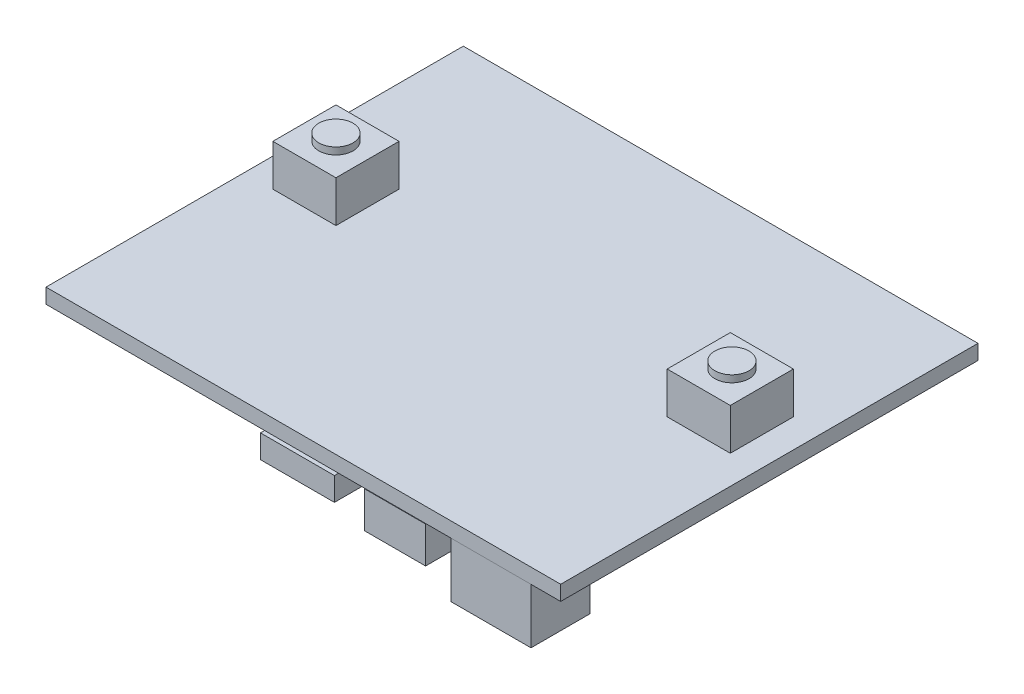
SolidWorks part; units mm, degrees
ref_plane "Plan de face" through (0, 0, 0) normal (0, 0, 1) x (1, 0, 0)
ref_plane "Plan de dessus" through (0, 0, 0) normal (0, 1, 0) x (1, 0, 0)
ref_plane "Plan de droite" through (0, 0, 0) normal (1, 0, 0) x (0, 0, -1)
sketch "Esquisse1" plane through (0, 0, 0) normal (0, 1, 0) x (1, 0, 0)
  line L1 (0, 0) -> (51.8, 0)
  line L2 (0, 0) -> (0, 42)
  line L3 (0, 42) -> (51.8, 42)
  line L4 (51.8, 0) -> (51.8, 42)
extrude "Boss.-Extru.1" add sketch "Esquisse1" against normal blind 1.5 contours L4 L3 L2 L1
sketch "Esquisse2" plane through (0, 0, 0) normal (0, 1, 0) x (1, 0, 0)
  line L0 (42.57, 26.3) -> (48.92, 26.3)
  line L1 (2.88, 26.3) -> (9.23, 26.3)
  line L2 (2.88, 26.3) -> (2.88, 19.95)
  line L3 (2.88, 19.95) -> (9.23, 19.95)
  line L4 (9.23, 26.3) -> (9.23, 19.95)
  line L5 (42.57, 26.3) -> (42.57, 19.95)
  line L6 (42.57, 19.95) -> (48.92, 19.95)
  line L7 (48.92, 26.3) -> (48.92, 19.95)
  line L8 (0, 42) -> (51.8, 42) construction
  line L9 (51.8, 0) -> (51.8, 42) construction
  line L10 (0, 0) -> (0, 42) construction
  dimension "D1" = 15.7
  dimension "D2" = 15.7
  dimension "D3" = 2.88
  dimension "D4" = 2.88
extrude "Boss.-Extru.2" add sketch "Esquisse2" along normal blind 4.17
sketch "Esquisse3" plane through (0, 4.17, 0) normal (0, 1, 0) x (1, 0, 0)
  circle A0 centre (6.0305, 23.1489) radius 1.72
  circle A1 centre (45.817, 23.2179) radius 1.72
extrude "Boss.-Extru.3" add sketch "Esquisse3" along normal blind 0.7
sketch "Esquisse5" plane through (0, -1.5, 0) normal (0, -1, 0) x (1, 0, 0)
  line L0 (0, 0) -> (0, -42) construction
  line L1 (22, 0.4133) -> (29.44, 0.4133)
  line L2 (22, 0.4133) -> (22, -5.4867)
  line L3 (22, -5.4867) -> (29.44, -5.4867)
  line L4 (29.44, 0.4133) -> (29.44, -5.4867)
  dimension "D1" = 22
sketch "Esquisse6" plane through (0, -1.5, 0) normal (0, -1, 0) x (1, 0, 0)
  line L0 (51.8, 0) -> (51.8, -42) construction
  line L1 (48.8, -5.9312) -> (40.76, -5.9312)
  line L2 (48.8, -5.9312) -> (48.8, -0.0112)
  line L3 (48.8, -0.0112) -> (40.76, -0.0112)
  line L4 (40.76, -5.9312) -> (40.76, -0.0112)
  dimension "D1" = 3
sketch "Esquisse7" plane through (0, -1.5, 0) normal (0, -1, 0) x (1, 0, 0)
  line L1 (32.0947, -6.1087) -> (38.2547, -6.1087)
  line L2 (32.0947, -6.1087) -> (32.0947, 0.0513)
  line L3 (32.0947, 0.0513) -> (38.2547, 0.0513)
  line L4 (38.2547, -6.1087) -> (38.2547, 0.0513)
extrude "Boss.-Extru.4" add sketch "Esquisse7" along normal blind 3.66
extrude "Boss.-Extru.5" add sketch "Esquisse5" along normal blind 2.34
extrude "Boss.-Extru.6" add sketch "Esquisse6" along normal blind 5.55
sketch "Esquisse8" plane through (0, -5.16, 0) normal (0, -1, 0) x (1, 0, 0)
  circle A0 centre (35.263, -2.9943) radius 1.72
extrude "Boss.-Extru.7" add sketch "Esquisse8" along normal blind 0.8
